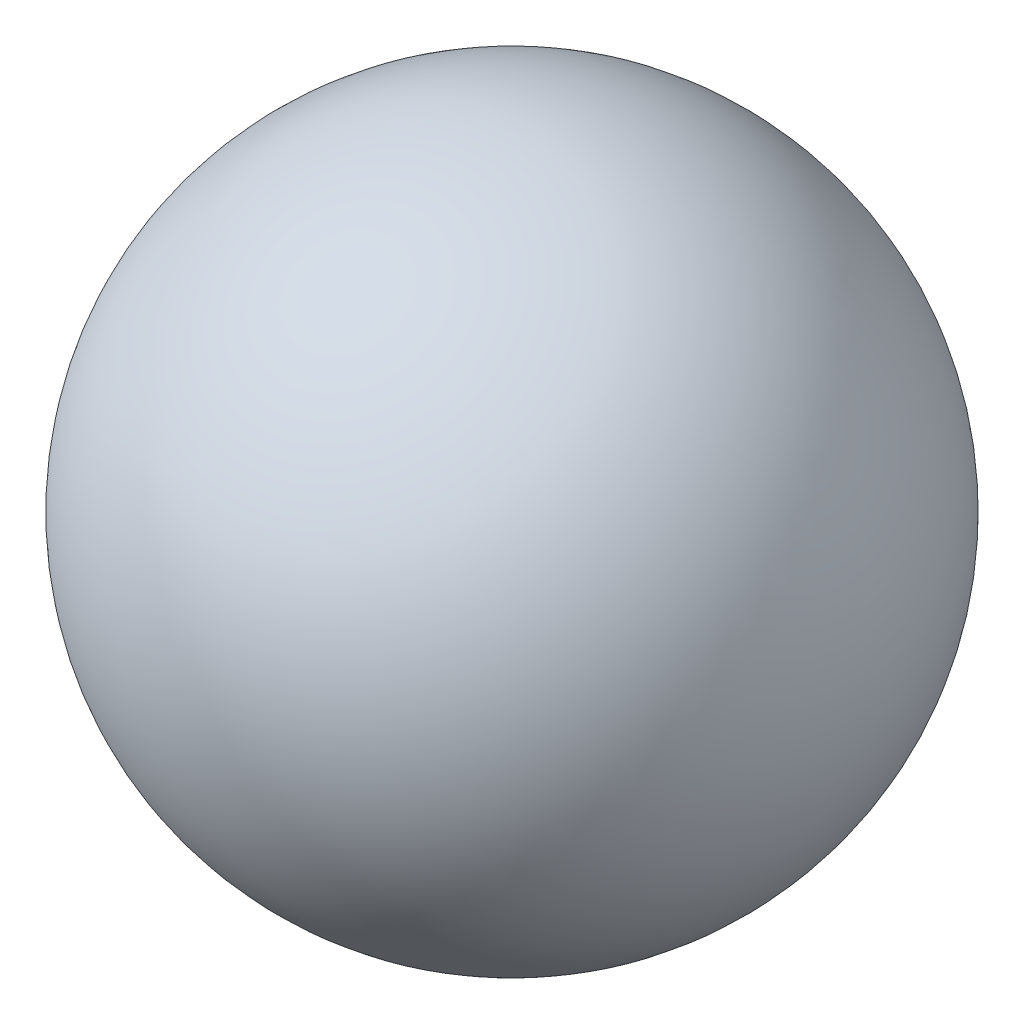
SolidWorks part; units mm, degrees
material "Natural Rubber"
ref_plane "Front Plane" through (0, 0, 0) normal (0, 0, 1) x (1, 0, 0)
ref_plane "Top Plane" through (0, 0, 0) normal (0, 1, 0) x (1, 0, 0)
ref_plane "Right Plane" through (0, 0, 0) normal (1, 0, 0) x (0, 0, -1)
sketch "Sketch1" plane through (0, 0, 0) normal (0, 0, 1) x (1, 0, 0)
  line L0 (0, -100) -> (0, 100) construction
  line L1 (0, 100) -> (0, -100)
  arc A0 (0, 100) -> (0, -100) centre (0, 0) cw
  point P4 (0, 0)
  dimension "D1" = 200
revolve "Revolve1" add sketch "Sketch1" angle 360 about L0
